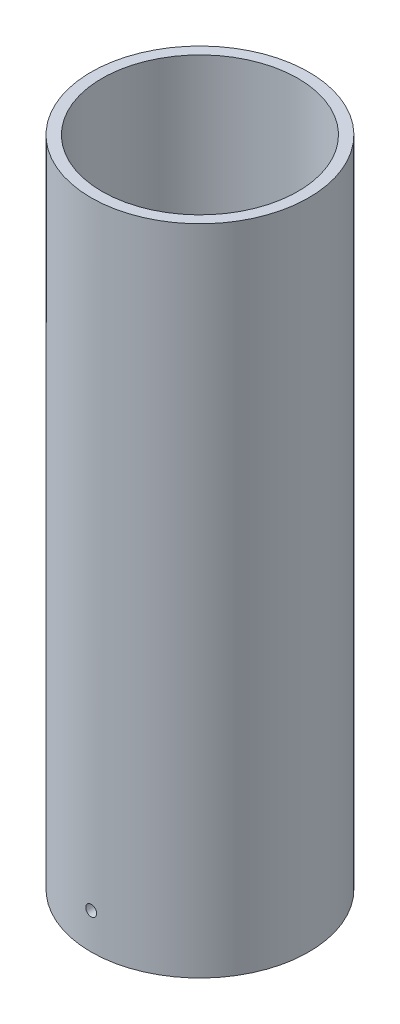
SolidWorks part; units mm, degrees
ref_plane "Front Plane" through (0, 0, 0) normal (0, 0, 1) x (1, 0, 0)
ref_plane "Top Plane" through (0, 0, 0) normal (0, 1, 0) x (1, 0, 0)
ref_plane "Right Plane" through (0, 0, 0) normal (1, 0, 0) x (0, 0, -1)
sketch "Sketch1" plane through (0, 0, 0) normal (0, 1, 0) x (1, 0, 0)
  circle A0 centre (0, 0) radius 30
  circle A1 centre (0, 0) radius 25
  dimension "D1" = 60
  dimension "D2" = 50
extrude "Boss-Extrude1" add sketch "Sketch1" along normal blind 180
sketch "Sketch2" plane through (0, 0, 0) normal (0, 0, 1) x (1, 0, 0)
  line L0 (0, 0) -> (0, 9.9) construction
  circle A0 centre (0, 9.9) radius 1.5
  dimension "D2" = 3
  dimension "D1" = 9.9
extrude "Cut-Extrude1" cut sketch "Sketch2" against normal through all and the other way through all
sketch "Sketch3" plane through (0, 180, 0) normal (0, 1, 0) x (1, 0, 0)
  circle A0 centre (0, 0) radius 19.5698
  circle A1 centre (0, 0) radius 27
extrude "Cut-Extrude2" cut sketch "Sketch3" against normal blind 160
